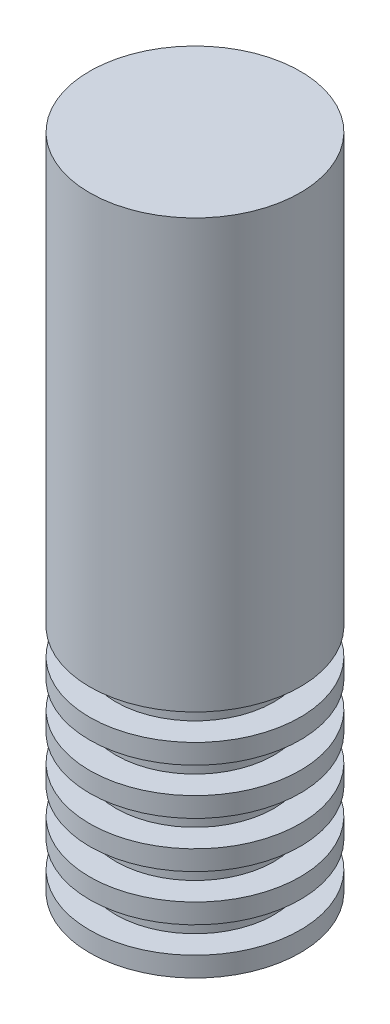
SolidWorks part; units mm, degrees
ref_plane "Alzado" through (0, 0, 0) normal (0, 0, 1) x (1, 0, 0)
ref_plane "Planta" through (0, 0, 0) normal (0, 1, 0) x (1, 0, 0)
ref_plane "Vista lateral" through (0, 0, 0) normal (1, 0, 0) x (0, 0, -1)
sketch "Croquis1" plane through (0, 0, 0) normal (0, 0, 1) x (1, 0, 0)
  line L0 (0, 68.764) -> (0, -16.4494) construction
  line L1 (0, 50) -> (8, 50)
  line L2 (0, 50) -> (0, 0)
  line L3 (4, 0) -> (8, 0)
  line L4 (8, 50) -> (8, 17.5)
  line L5 (8, 8.5) -> (8, 7)
  line L6 (8, 1.5) -> (6, 1.5)
  line L7 (8, 15.5) -> (8, 14)
  line L8 (8, 3.5) -> (6, 3.5)
  line L9 (6, 1.5) -> (6, 3.5)
  line L10 (8, 5) -> (6, 5)
  line L11 (8, 1.5) -> (8, 0)
  line L12 (8, 7) -> (6, 7)
  line L13 (6, 5) -> (6, 7)
  line L14 (8, 8.5) -> (6, 8.5)
  line L15 (8, 5) -> (8, 3.5)
  line L16 (8, 10.5) -> (6, 10.5)
  line L17 (6, 8.5) -> (6, 10.5)
  line L18 (8, 14) -> (6, 14)
  line L19 (0, 0) -> (0, -2)
  line L20 (0, -2) -> (4, -2)
  line L21 (4, 0) -> (4, -2)
  line L23 (8, 12) -> (6, 12)
  line L24 (6, 14) -> (6, 12)
  line L25 (8, 17.5) -> (6, 17.5)
  line L26 (8, 12) -> (8, 10.5)
  line L27 (8, 15.5) -> (6, 15.5)
  line L28 (6, 17.5) -> (6, 15.5)
  dimension "D1" = 16
  dimension "D2" = 50
  dimension "D3" = 1.5
  dimension "D4" = 2
  dimension "D5" = 1.5
  dimension "D6" = 1.5
  dimension "D7" = 2
  dimension "D8" = 8
  dimension "D9" = 2
revolve "Revolución1" add sketch "Croquis1" angle 360 about L0
